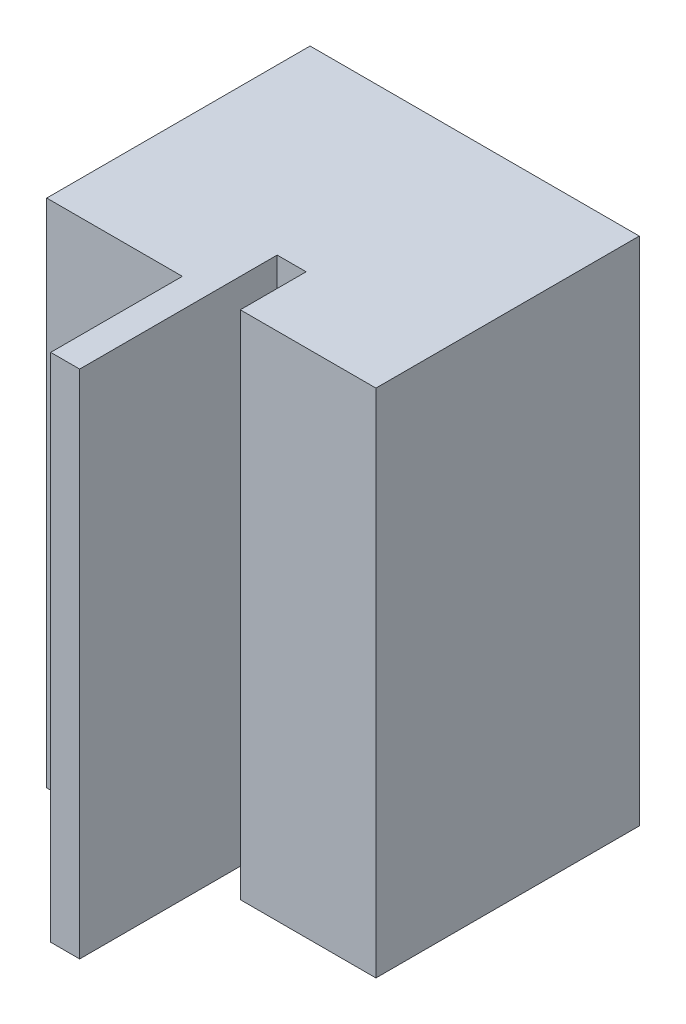
SolidWorks part; units mm, degrees
ref_plane "前基準面" through (0, 0, 0) normal (0, 0, 1) x (1, 0, 0)
ref_plane "上基準面" through (0, 0, 0) normal (0, 1, 0) x (1, 0, 0)
ref_plane "右基準面" through (0, 0, 0) normal (1, 0, 0) x (0, 0, -1)
sketch "草圖1" plane through (0, 0, 0) normal (0, 1, 0) x (1, 0, 0)
  line L1 (-12.5, -10) -> (12.5, -10)
  line L2 (-12.5, -10) -> (-12.5, 10)
  line L3 (-12.5, 10) -> (12.5, 10)
  line L4 (12.5, -10) -> (12.5, 10)
  line L5 (-12.5, -10) -> (12.5, 10) construction
  line L6 (-12.5, 10) -> (12.5, -10) construction
  point P0 (0, 0)
  dimension "D1" = 20
  dimension "D2" = 25
extrude "填料-伸長1" add sketch "草圖1" along normal blind 38.8
sketch "草圖3" plane through (0, 38.8, 0) normal (0, 1, 0) x (1, 0, 0)
  line L0 (-12.5, -10) -> (12.5, -10) construction
  line L1 (0, -10) -> (0, -20) construction
  line L3 (-2.2, -20) -> (2.2, -20)
  line L4 (-2.2, -20) -> (-2.2, -10)
  line L5 (-2.2, -10) -> (2.2, -10)
  line L6 (2.2, -20) -> (2.2, -10)
  line L7 (-2.2, -20) -> (2.2, -10) construction
  line L8 (-2.2, -10) -> (2.2, -20) construction
  point P7 (0, -15)
  dimension "D1" = 10
  dimension "D2" = 4.4
extrude "填料-伸長2" add sketch "草圖3" against normal blind 38.8
sketch "草圖5" plane through (2.2, 0, 0) normal (1, 0, 0) x (0, 0, -1)
  line L0 (-10, 0) -> (10, 0) construction
  line L5 (-20, 38.8) -> (-5, 38.8)
  line L6 (-20, 38.8) -> (-20, 0)
  line L7 (-20, 0) -> (-5, 0)
  line L8 (-5, 38.8) -> (-5, 0)
  dimension "D1" = 15
extrude "除料-伸長2" cut sketch "草圖5" against normal blind 2.2
